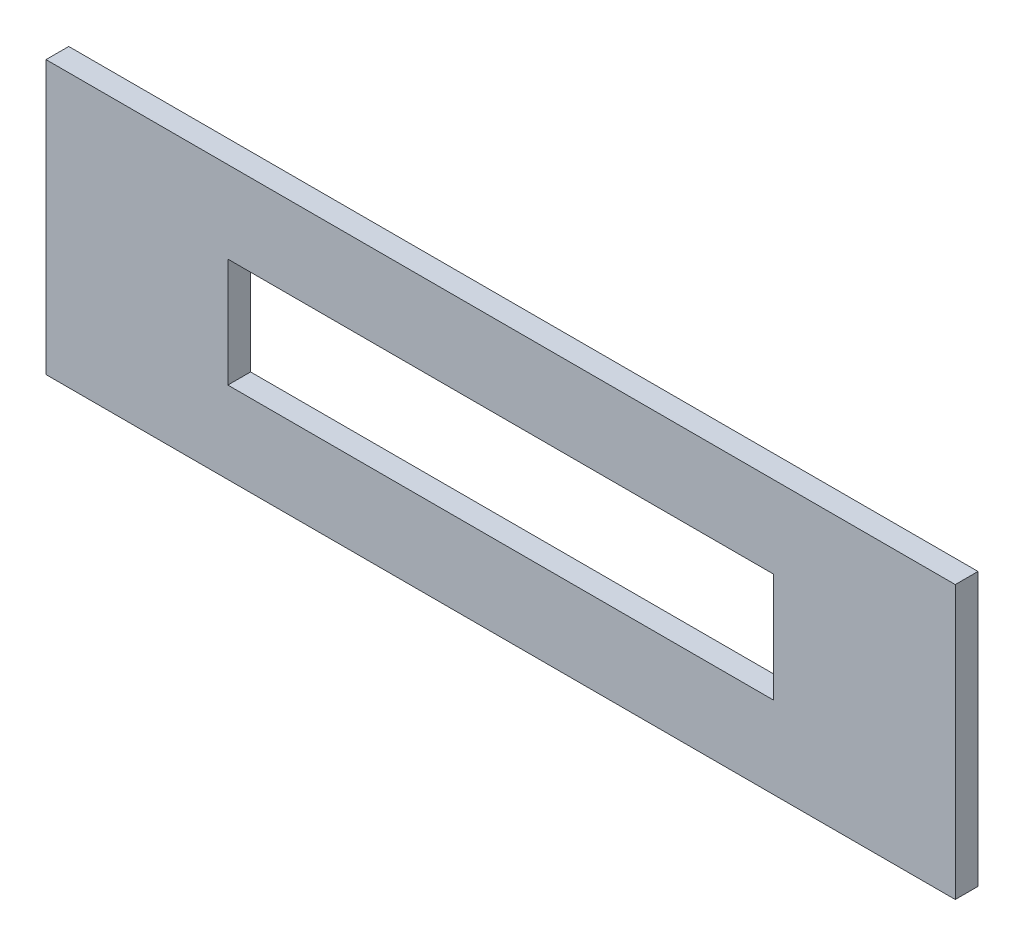
SolidWorks part; units mm, degrees
material "Test"
ref_plane "Front Plane" through (0, 0, 0) normal (0, 0, 1) x (1, 0, 0)
ref_plane "Top Plane" through (0, 0, 0) normal (0, 1, 0) x (1, 0, 0)
ref_plane "Right Plane" through (0, 0, 0) normal (1, 0, 0) x (0, 0, -1)
sketch "Sketch1" plane through (0, 0, 0) normal (0, 0, 1) x (1, 0, 0)
  line L5 (-200, 60) -> (200, 60)
  line L6 (-200, 60) -> (-200, -60)
  line L7 (-200, -60) -> (200, -60)
  line L8 (200, 60) -> (200, -60)
  line L9 (-200, 60) -> (200, -60) construction
  line L10 (-200, -60) -> (200, 60) construction
  line L11 (-120, 24) -> (120, 24)
  line L12 (-120, 24) -> (-120, -24)
  line L13 (-120, -24) -> (120, -24)
  line L14 (120, 24) -> (120, -24)
  line L15 (-120, 24) -> (120, -24) construction
  line L16 (-120, -24) -> (120, 24) construction
  point P0 (0, 0)
  point P7 (0, 0)
  dimension "D1" = 120
  dimension "D2" = 400
  dimension "D3" = 240
  dimension "D4" = 48
extrude "Boss-Extrude1" add sketch "Sketch1" along normal blind 10
sketch "Sketch2" plane through (200, 0, 0) normal (1, 0, 0) x (0, 0, -1)
  line L0 (-10, 0) -> (0, 0) construction
  line L1 (-10, -60) -> (-10, 60) construction
  point P5 (-5, 0)
